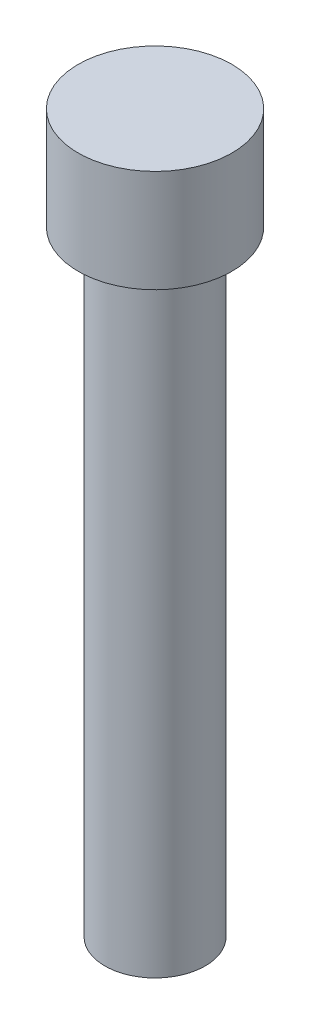
SolidWorks part; units mm, degrees
ref_plane "Front Plane" through (0, 0, 0) normal (0, 0, 1) x (1, 0, 0)
ref_plane "Top Plane" through (0, 0, 0) normal (0, 1, 0) x (1, 0, 0)
ref_plane "Right Plane" through (0, 0, 0) normal (1, 0, 0) x (0, 0, -1)
sketch "Sketch1" plane through (0, 0, 0) normal (0, 0, 1) x (1, 0, 0)
  line L0 (4.7625, 44.45) -> (0, 44.45)
  line L1 (0, 44.45) -> (0, 0)
  line L2 (0, 0) -> (3.1115, 0)
  line L3 (3.1115, 0) -> (3.1115, 38.1)
  line L4 (3.1115, 38.1) -> (4.7625, 38.1)
  line L5 (4.7625, 38.1) -> (4.7625, 44.45)
  line L6 (0, 44.45) -> (0, 0) construction
revolve "Revolve1" add sketch "Sketch1" angle 360 about L6
